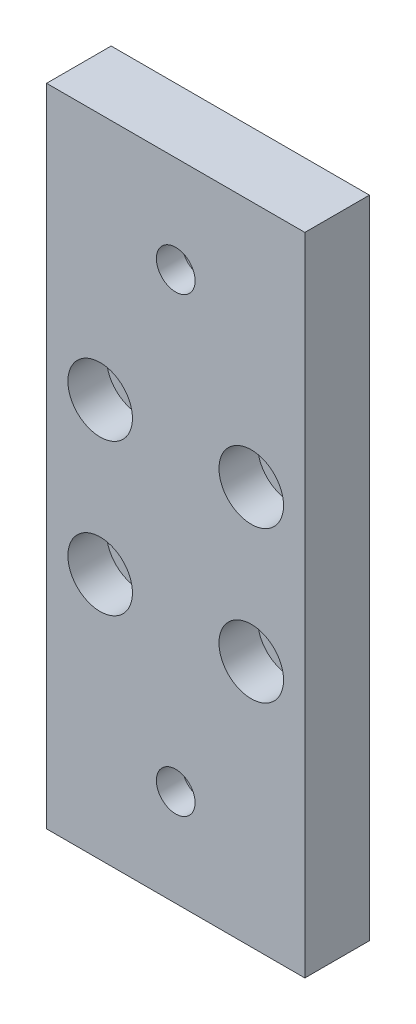
SolidWorks part; units mm, degrees
ref_plane "Front Plane" through (0, 0, 0) normal (0, 0, 1) x (1, 0, 0)
ref_plane "Top Plane" through (0, 0, 0) normal (0, 1, 0) x (1, 0, 0)
ref_plane "Right Plane" through (0, 0, 0) normal (1, 0, 0) x (0, 0, -1)
sketch "Sketch1" plane through (0, 0, 0) normal (0, 0, 1) x (1, 0, 0)
  line L0 (0, 0) -> (40, 0)
  line L7 (0, 100) -> (40, 100)
  line L8 (40, 0) -> (40, 100)
  line L14 (0, 100) -> (0, 0)
  dimension "D1" = 40
  dimension "D4" = 100
extrude "Boss-Extrude1" add sketch "Sketch1" along normal blind 10
sketch "Sketch3" plane through (0, 0, 10) normal (0, 0, 1) x (1, 0, 0)
  line L0 (0, 0) -> (40, 0) construction
  line L1 (8.3, 38.3) -> (31.7, 38.3) construction
  line L2 (8.3, 38.3) -> (8.3, 61.7) construction
  line L3 (8.3, 61.7) -> (31.7, 61.7) construction
  line L4 (31.7, 38.3) -> (31.7, 61.7) construction
  line L5 (20, 61.7) -> (20, 38.3) construction
  line L6 (8.3, 50) -> (31.7, 50) construction
  line L7 (0, 100) -> (0, 0) construction
  circle A0 centre (8.3, 61.7) radius 2.5
  circle A1 centre (31.7, 61.7) radius 2.5
  circle A2 centre (31.7, 38.3) radius 2.5
  circle A3 centre (8.3, 38.3) radius 2.5
  point P0 (20, 50)
  point P7 (20, 0)
  point P10 (0, 50)
  dimension "D3" = 5
  dimension "D1" = 23.4
  dimension "D2" = 23.4
extrude "Cut-Extrude1" cut sketch "Sketch3" against normal blind 40
sketch "Sketch4" plane through (0, 0, 10) normal (0, 0, 1) x (1, 0, 0)
  circle A0 centre (8.3, 61.7) radius 5
  circle A1 centre (31.7, 61.7) radius 5
  circle A2 centre (31.7, 38.3) radius 5
  circle A3 centre (8.3, 38.3) radius 5
  dimension "D1" = 10
extrude "Cut-Extrude2" cut sketch "Sketch4" against normal blind 6
sketch "Sketch6" plane through (0, 0, 0) normal (0, 0, -1) x (-1, 0, 0)
  line L0 (-20, 100) -> (-20, 0) construction
  line L1 (-40, 100) -> (0, 100) construction
  line L2 (0, 0) -> (-40, 0) construction
  line L3 (-20, 15) -> (-16.1421, 15) construction
  line L4 (-16.1421, 15) -> (-16.1421, 0) construction
  line L5 (-20, 85) -> (-24.9663, 85) construction
  line L6 (-24.9663, 85) -> (-24.9663, 100) construction
  circle A0 centre (-20, 85) radius 5
  circle A1 centre (-20, 15) radius 5
  dimension "D2" = 10
  dimension "D1" = 15
extrude "Cut-Extrude3" cut sketch "Sketch6" against normal blind 6
sketch "Sketch7" plane through (0, 0, 6) normal (0, 0, -1) x (-1, 0, 0)
  circle A0 centre (-20, 15) radius 3
  circle A1 centre (-20, 85) radius 3
  dimension "D1" = 6
extrude "Cut-Extrude4" cut sketch "Sketch7" against normal through all
